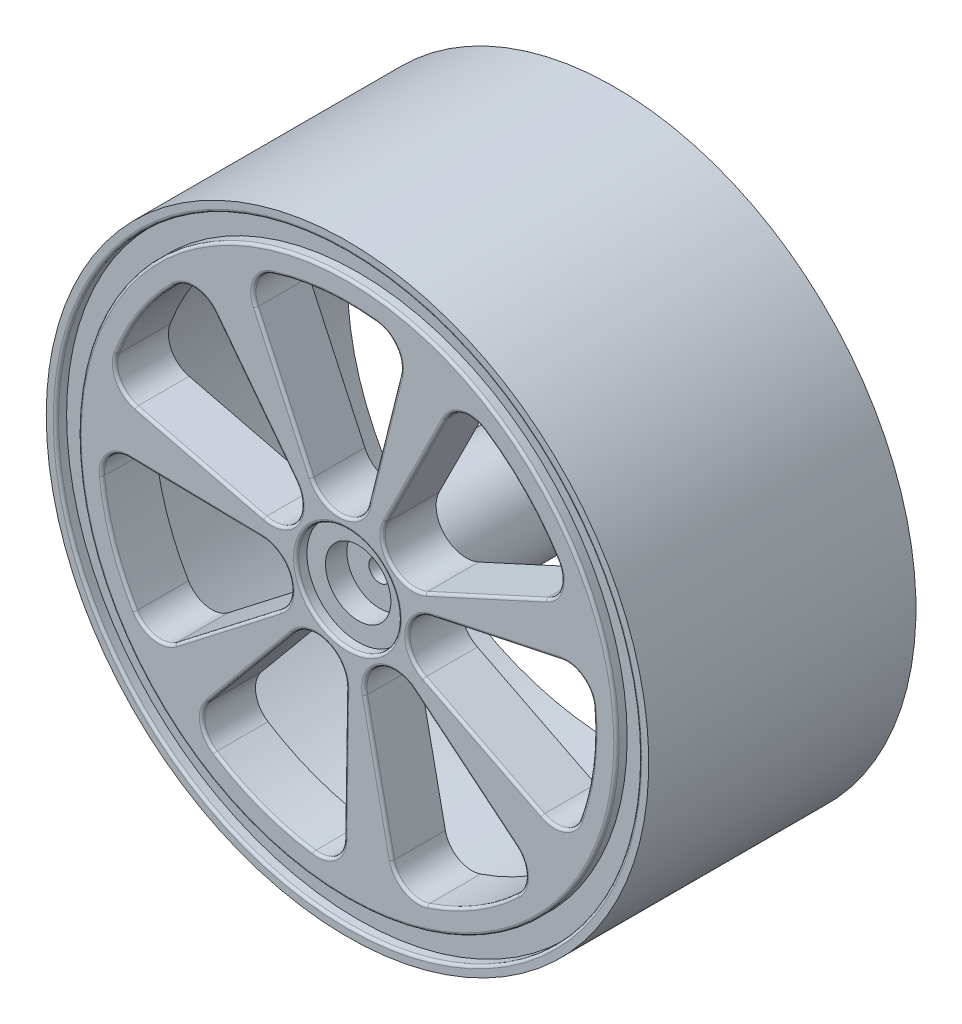
SolidWorks part; units mm, degrees
material "3.0517 (EN-AW 3003)"
ref_plane "前视基准面" through (0, 0, 0) normal (0, 0, 1) x (1, 0, 0)
ref_plane "上视基准面" through (0, 0, 0) normal (0, 1, 0) x (1, 0, 0)
ref_plane "右视基准面" through (0, 0, 0) normal (1, 0, 0) x (0, 0, -1)
sketch "Model" plane through (0, 0, 0) normal (0, 0, 1) x (1, 0, 0)
  line L0 (796.1708, 277.6799) -> (798.8531, 278.2865)
  arc A0 (796.1708, 277.6799) -> (798.8531, 278.2865) centre (797.8323, 276.5666) ccw
  circle A1 centre (797.8323, 276.5666) radius 5
  dimension "D1" = 2
  dimension "D2" = 10
extrude "凸台-拉伸1" add sketch "Model" along normal blind 20 contours L0 A0 | A1
sketch "草图2" plane through (0, 0, 20) normal (0, 0, 1) x (1, 0, 0)
  circle A0 centre (797.8323, 276.5666) radius 33
  dimension "D1" = 66
extrude "凸台-拉伸2" add sketch "草图2" along normal blind 5
sketch "草图3" plane through (0, 0, 20) normal (0, 0, -1) x (-1, 0, 0)
  circle A0 centre (-797.8323, 276.5666) radius 25
  circle A1 centre (-797.8323, 276.5666) radius 33
  dimension "D1" = 50
  dimension "D2" = 66
extrude "凸台-拉伸3" add sketch "草图3" along normal up to vertex (20 mm away)
sketch "草图4" plane through (0, 0, 0) normal (0, 0, -1) x (-1, 0, 0)
  circle A0 centre (-797.8323, 276.5666) radius 28.1902
  circle A1 centre (-797.8323, 276.5666) radius 33
extrude "切除-拉伸1" cut sketch "草图4" against normal blind 25
sketch "草图5" plane through (0, 0, 25) normal (0, 0, 1) x (1, 0, 0)
  circle A0 centre (797.8323, 276.5666) radius 3.0616
extrude "切除-拉伸3" cut sketch "草图5" against normal blind 3
sketch "草图6" plane through (0, 0, 25) normal (0, 0, 1) x (1, 0, 0)
  circle A0 centre (797.8323, 276.5666) radius 4.8003
extrude "切除-拉伸4" cut sketch "草图6" against normal blind 1
sketch "草图7" plane through (0, 0, 22) normal (0, 0, 1) x (1, 0, 0)
  circle A0 centre (797.8323, 276.5666) radius 1
  dimension "D1" = 2
extrude "切除-拉伸5" cut sketch "草图7" against normal blind 40
sketch "草图8" plane through (0, 0, 25) normal (0, 0, 1) x (1, 0, 0)
  line L0 (790.0421, 278.4681) -> (778.0122, 281.4044)
  line L1 (792.9545, 282.9314) -> (785.422, 292.76)
  line L2 (799.7672, 284.3486) -> (802.755, 296.3658)
  line L3 (794.4618, 283.8428) -> (789.257, 295.0789)
  line L4 (805.1229, 279.9059) -> (816.3812, 285.0625)
  line L5 (801.4196, 283.7384) -> (806.9592, 294.8133)
  line L6 (804.9887, 272.9486) -> (816.0397, 267.3616)
  line L7 (805.6761, 278.2335) -> (817.7887, 280.8076)
  line L8 (799.4656, 268.7158) -> (801.9877, 256.5923)
  line L9 (804.026, 271.4734) -> (813.5906, 263.6083)
  line L10 (792.7126, 270.3948) -> (784.8066, 260.8641)
  line L11 (797.712, 268.5486) -> (797.5262, 256.1669)
  line L12 (789.8149, 276.7213) -> (777.4341, 276.9602)
  line L13 (791.4886, 271.6616) -> (781.6924, 264.087)
  arc A0 (776.2403, 284.7745) -> (781.6236, 293.0246) centre (797.8323, 276.5666) cw
  arc A1 (790.0421, 278.4681) -> (792.9545, 282.9314) centre (790.712, 281.2128) ccw
  arc A2 (785.422, 292.76) -> (781.6236, 293.0246) centre (783.4059, 291.2149) ccw
  arc A3 (778.0122, 281.4044) -> (776.2403, 284.7745) centre (778.6145, 283.872) cw
  arc A4 (790.7871, 298.5655) -> (800.5937, 299.5005) centre (797.8323, 276.5666) cw
  arc A5 (802.755, 296.3658) -> (800.5937, 299.5005) centre (800.2901, 296.9787) ccw
  arc A6 (794.4618, 283.8428) -> (799.7672, 284.3486) centre (797.0254, 285.0303) ccw
  arc A7 (789.257, 295.0789) -> (790.7871, 298.5655) centre (791.5618, 296.1465) cw
  arc A8 (810.6391, 295.7909) -> (817.4844, 288.7067) centre (797.8323, 276.5666) cw
  arc A9 (816.3812, 285.0625) -> (817.4844, 288.7067) centre (815.3235, 287.3718) ccw
  arc A10 (801.4196, 283.7384) -> (805.1229, 279.9059) centre (803.9464, 282.4745) ccw
  arc A11 (806.9592, 294.8133) -> (810.6391, 295.7909) centre (809.2309, 293.677) cw
  arc A12 (820.8474, 278.54) -> (819.5767, 268.7712) centre (797.8323, 276.5666) cw
  arc A13 (816.0397, 267.3616) -> (819.5767, 268.7712) centre (817.1857, 269.6284) ccw
  arc A14 (805.6761, 278.2335) -> (804.9887, 272.9486) centre (806.2634, 275.47) ccw
  arc A15 (817.7887, 280.8076) -> (820.8474, 278.54) centre (818.3166, 278.323) cw
  arc A16 (813.7248, 259.8031) -> (805.295, 254.7058) centre (797.8323, 276.5666) cw
  arc A17 (801.9877, 256.5923) -> (805.295, 254.7058) centre (804.4744, 257.1096) ccw
  arc A18 (804.026, 271.4734) -> (799.4656, 268.7158) centre (802.2316, 269.2912) ccw
  arc A19 (813.5906, 263.6083) -> (813.7248, 259.8031) centre (811.9773, 261.6464) cw
  arc A20 (794.6349, 253.6895) -> (785.3938, 257.1021) centre (797.8323, 276.5666) cw
  arc A21 (784.8066, 260.8641) -> (785.3938, 257.1021) centre (786.7615, 259.2424) ccw
  arc A22 (797.712, 268.5486) -> (792.7126, 270.3948) centre (794.8871, 268.591) ccw
  arc A23 (797.5262, 256.1669) -> (794.6349, 253.6895) centre (794.9865, 256.2051) cw
  arc A24 (777.9527, 264.8028) -> (774.859, 274.1555) centre (797.8323, 276.5666) cw
  arc A25 (777.4341, 276.9602) -> (774.859, 274.1555) centre (777.3851, 274.4207) ccw
  arc A26 (791.4886, 271.6616) -> (789.8149, 276.7213) centre (789.7604, 273.8966) ccw
  arc A27 (781.6924, 264.087) -> (777.9527, 264.8028) centre (780.1387, 266.0964) cw
  point P68 (797.8323, 276.5666)
  dimension "D1" = 2.54
  dimension "D2" = 7
extrude "切除-拉伸6" cut sketch "草图8" against normal blind 40
fillet "圆角1" radius 0.25 1 edges at (802.6327, 276.5666, 25)
fillet "圆角3" radius 0.25 6 edges at (817.7545, 286.6358, 25) (814.4438, 292.618, 25) (808.5787, 296.1319, 25) (804.1894, 289.2759, 25) (801.9147, 280.5113, 25) (810.7521, 282.4842, 25)
fillet "圆角4" radius 0.25 6 edges at (802.3812, 298.4205, 25) (795.64, 299.5619, 25) (789.2359, 297.1672, 25) (791.8594, 289.4609, 25) (797.2935, 282.2178, 25) (801.2611, 290.3572, 25)
fillet "圆角5" radius 0.25 6 edges at (783.5825, 293.7488, 25) (778.487, 289.1899, 25) (776.3663, 282.6899, 25) (784.0272, 279.9363, 25) (793.0781, 279.6689, 25) (789.1882, 287.8457, 25)
fillet "圆角6" radius 0.25 6 edges at (775.5142, 276.1385, 25) (775.9015, 269.3123, 25) (779.6611, 263.6016, 25) (786.5905, 267.8743, 25) (792.4427, 274.7839, 25) (783.6245, 276.8408, 25)
fillet "圆角7" radius 0.25 6 edges at (784.2519, 258.8507, 25) (789.8303, 254.8974, 25) (796.6392, 254.2763, 25) (797.6191, 262.3578, 25) (795.8658, 271.2413, 25) (788.7596, 265.6294, 25)
fillet "圆角8" radius 0.25 6 edges at (803.216, 254.9033, 25) (809.7848, 256.7999, 25) (814.5157, 261.736, 25) (808.8083, 267.5409, 25) (800.7697, 271.7089, 25) (800.7266, 262.6541, 25)
fillet "圆角9" radius 0.25 6 edges at (818.126, 267.2689, 25) (820.7388, 273.5871, 25) (819.8293, 280.3635, 25) (811.7324, 279.5205, 25) (803.4617, 275.8344, 25) (810.5142, 270.1551, 25)
sketch "草图9" plane through (0, 0, 25) normal (0, 0, 1) x (1, 0, 0)
  circle A0 centre (797.8323, 276.5666) radius 25.1694
  circle A1 centre (797.8323, 276.5666) radius 27.2847
extrude "切除-拉伸7" cut sketch "草图9" against normal blind 1
fillet "圆角10" radius 0.25 1 edges at (825.117, 276.5666, 25)
fillet "圆角11" radius 0.25 1 edges at (823.0017, 276.5666, 25)
